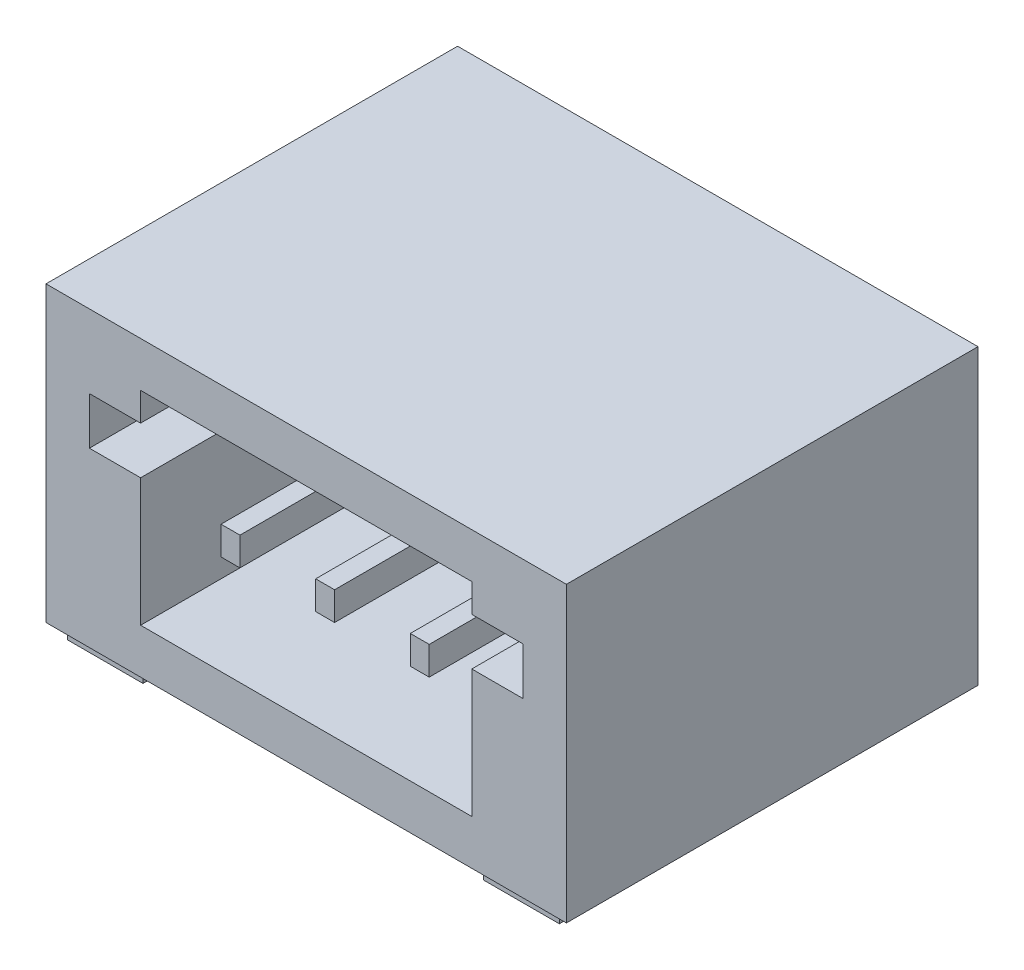
SolidWorks part; units mm, degrees
ref_plane "前视基准面" through (0, 0, 0) normal (0, 0, 1) x (1, 0, 0)
ref_plane "上视基准面" through (0, 0, 0) normal (0, 1, 0) x (1, 0, 0)
ref_plane "右视基准面" through (0, 0, 0) normal (1, 0, 0) x (0, 0, -1)
sketch "草图1" plane through (0, 0, 0) normal (1, 0, 0) x (0, 0, -1)
  line L1 (0, 0) -> (4.35, 0)
  line L2 (0, 0) -> (0, 3.1)
  line L3 (0, 3.1) -> (4.35, 3.1)
  line L4 (4.35, 0) -> (4.35, 3.1)
  dimension "D1" = 4.35
  dimension "D2" = 3.1
extrude "凸台-拉伸1" add sketch "草图1" along normal blind 5.5
sketch "草图2" plane through (0, 0, 0) normal (0, 0, 1) x (1, 0, 0)
  line L0 (2.75, 0) -> (2.75, 3.1) construction
  line L1 (5.5, 0) -> (0, 0) construction
  line L2 (5.5, 3.1) -> (0, 3.1) construction
  line L3 (1, 0.475) -> (4.5, 0.475)
  line L4 (4.5, 0.475) -> (4.5, 1.825)
  line L5 (4.5, 1.825) -> (5.0413, 1.825)
  line L6 (5.0413, 1.825) -> (5.0413, 2.325)
  line L7 (5.0413, 2.325) -> (4.5, 2.325)
  line L8 (4.5, 2.325) -> (4.5, 2.625)
  line L9 (4.5, 2.625) -> (1, 2.625)
  line L10 (1, 0.475) -> (1, 1.825)
  line L11 (1, 1.825) -> (0.4587, 1.825)
  line L12 (0.4587, 1.825) -> (0.4587, 2.325)
  line L13 (0.4587, 2.325) -> (1, 2.325)
  line L14 (1, 2.325) -> (1, 2.625)
  point P15 (2.75, 0.475)
  point P20 (2.75, 2.625)
  dimension "D1" = 2.15
  dimension "D2" = 3.5
  dimension "D3" = 0.475
  dimension "D4" = 0.475
  dimension "D5" = 0.5
  dimension "D6" = 0.3
extrude "切除-拉伸1" cut sketch "草图2" against normal blind 3.7
sketch "草图4" plane through (0, 0, -3.7) normal (0, 0, 1) x (1, 0, 0)
  line L0 (0, 1.175) -> (5.5, 1.175) construction
  line L1 (0, 3.1) -> (0, 0) construction
  line L2 (5.5, 3.1) -> (5.5, 0) construction
  line L3 (2.65, 1.625) -> (2.65, 1.325)
  line L4 (1.65, 1.625) -> (1.85, 1.625)
  line L5 (1.65, 1.625) -> (1.65, 1.325)
  line L6 (1.65, 1.325) -> (1.85, 1.325)
  line L7 (1.85, 1.625) -> (1.85, 1.325)
  line L8 (2.65, 1.625) -> (2.85, 1.625)
  line L9 (2.85, 1.625) -> (2.85, 1.325)
  line L10 (2.65, 1.325) -> (2.85, 1.325)
  line L11 (3.65, 1.625) -> (3.65, 1.325)
  line L12 (3.65, 1.625) -> (3.85, 1.625)
  line L13 (3.85, 1.625) -> (3.85, 1.325)
  line L14 (3.65, 1.325) -> (3.85, 1.325)
  line L15 (1, 0.475) -> (4.5, 0.475) construction
  point P11 (2.75, 1.325)
  point P19 (2.75, 1.175)
  dimension "D1" = 0.2
  dimension "D2" = 0.3
  dimension "D4" = 0.7
  dimension "D5" = 0.15
  dimension "D3" = 3
extrude "凸台-拉伸2" add sketch "草图4" along normal blind 3.5
sketch "草图5" plane through (0, 0, 0) normal (0, -1, 0) x (1, 0, 0)
  line L0 (0, -2.175) -> (5.5, -2.175) construction
  line L1 (0, 0) -> (0, -4.35) construction
  line L2 (5.5, 0) -> (5.5, -4.35) construction
  line L3 (2.75, -2.175) -> (2.75, 0) construction
  line L4 (5.5, 0) -> (0, 0) construction
  line L5 (2.65, -4.175) -> (2.65, -5.025)
  line L6 (0.15, -0.075) -> (0.95, -0.075)
  line L7 (0.15, -0.075) -> (0.15, -1.375)
  line L8 (0.15, -1.375) -> (0.95, -1.375)
  line L9 (0.95, -0.075) -> (0.95, -1.375)
  line L10 (1.65, -4.175) -> (1.85, -4.175)
  line L11 (1.65, -4.175) -> (1.65, -5.025)
  line L12 (1.65, -5.025) -> (1.85, -5.025)
  line L13 (1.85, -4.175) -> (1.85, -5.025)
  line L14 (2.65, -4.175) -> (2.85, -4.175)
  line L15 (2.85, -4.175) -> (2.85, -5.025)
  line L16 (2.65, -5.025) -> (2.85, -5.025)
  line L17 (3.65, -4.175) -> (3.65, -5.025)
  line L18 (3.65, -4.175) -> (3.85, -4.175)
  line L19 (3.85, -4.175) -> (3.85, -5.025)
  line L20 (3.65, -5.025) -> (3.85, -5.025)
  line L21 (5.35, -1.375) -> (4.55, -1.375)
  line L22 (5.35, -0.075) -> (4.55, -0.075)
  line L23 (4.55, -0.075) -> (4.55, -1.375)
  line L24 (5.35, -0.075) -> (5.35, -1.375)
  point P19 (2.75, -4.175)
  dimension "D1" = 0.2
  dimension "D2" = 0.85
  dimension "D3" = 2
  dimension "D5" = 1.3
  dimension "D6" = 0.8
  dimension "D7" = 0.8
  dimension "D8" = 1.8
  dimension "D4" = 3
extrude "凸台-拉伸3" add sketch "草图5" along normal blind 0.12
